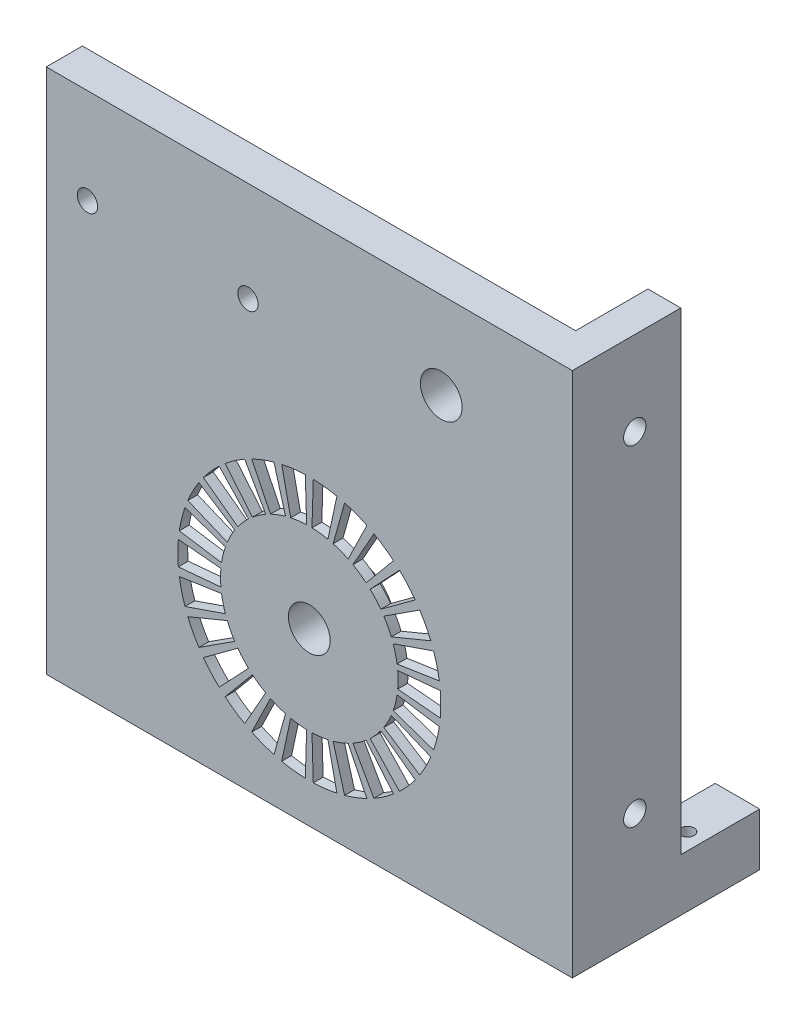
SolidWorks part; units mm, degrees
ref_plane "Front Plane" through (0, 0, 0) normal (0, 0, 1) x (1, 0, 0)
ref_plane "Top Plane" through (0, 0, 0) normal (0, 1, 0) x (1, 0, 0)
ref_plane "Right Plane" through (0, 0, 0) normal (1, 0, 0) x (0, 0, -1)
sketch "LED panel" plane through (0, 0, 0) normal (0, 0, 1) x (1, 0, 0)
  line L1 (-40, 40) -> (40, 40)
  line L2 (-40, 40) -> (-40, -40)
  line L3 (-40, -40) -> (40, -40)
  line L4 (40, 40) -> (40, -40)
  line L5 (-40, 40) -> (40, -40) construction
  line L6 (-40, -40) -> (40, 40) construction
  point P0 (0, 0)
  dimension "D1" = 80
  dimension "D2" = 80
extrude "Extrude LED panel" add sketch "LED panel" along normal blind 2.5
sketch "Sketch3" plane through (0, 0, 2.5) normal (0, 0, 1) x (1, 0, 0)
  circle A0 centre (0, -14) radius 5.9987
  circle A1 centre (20.0721, 26.7806) radius 6.0029
extrude "Boss-Extrude2" add sketch "Sketch3" against normal blind 7
sketch "Sketch1" plane through (0, 0, 2.5) normal (0, 0, 1) x (1, 0, 0)
  line L0 (-40, -14) -> (40, -14) construction
  line L3 (0, 40) -> (0, -40) construction
  line L4 (40, 40) -> (-40, 40) construction
  line L5 (-40, -40) -> (40, -40) construction
  line L6 (0, -14) -> (52.2337, -7.6577) construction
  line L7 (0, -14) -> (47.0949, -19.7184) construction
  line L8 (0, -14) -> (19.9179, -12.19) construction
  line L9 (0, -14) -> (41.9979, -17.8164) construction
  line L10 (13.4446, -12.7783) -> (19.9179, -12.19)
  line L11 (13.4446, -15.2217) -> (19.9179, -15.81)
  line L12 (13.3463, -16.0313) -> (19.7723, -17.0093)
  line L13 (12.7615, -18.4037) -> (18.906, -20.5241)
  line L14 (12.4724, -19.1662) -> (18.4776, -21.6537)
  line L15 (11.3368, -21.3298) -> (16.7953, -24.859)
  line L16 (10.8736, -22.0009) -> (16.109, -25.8532)
  line L17 (9.2533, -23.8299) -> (13.7085, -28.5628)
  line L18 (8.6429, -24.3707) -> (12.8043, -29.364)
  line L19 (6.6319, -25.7587) -> (9.8251, -31.4203)
  line L20 (5.9099, -26.1377) -> (8.7554, -31.9818)
  line L21 (3.6252, -27.0042) -> (5.3706, -33.2654)
  line L22 (2.8334, -27.1993) -> (4.1976, -33.5545)
  line L23 (0.4077, -27.4938) -> (0.6041, -33.9909)
  line L24 (-0.4077, -27.4938) -> (-0.6041, -33.9909)
  line L25 (-2.8334, -27.1993) -> (-4.1976, -33.5545)
  line L26 (-3.6252, -27.0042) -> (-5.3706, -33.2654)
  line L27 (-5.9099, -26.1377) -> (-8.7554, -31.9818)
  line L28 (-6.6319, -25.7587) -> (-9.8251, -31.4203)
  line L29 (-8.6429, -24.3707) -> (-12.8043, -29.364)
  line L30 (-9.2533, -23.8299) -> (-13.7085, -28.5628)
  line L31 (-10.8736, -22.0009) -> (-16.109, -25.8532)
  line L32 (-11.3368, -21.3298) -> (-16.7953, -24.859)
  line L33 (-12.4724, -19.1662) -> (-18.4776, -21.6537)
  line L34 (-12.7615, -18.4037) -> (-18.906, -20.5241)
  line L35 (-13.3463, -16.0313) -> (-19.7723, -17.0093)
  line L36 (-13.4446, -15.2217) -> (-19.9179, -15.81)
  line L37 (-13.4446, -12.7783) -> (-19.9179, -12.19)
  line L38 (-13.3463, -11.9687) -> (-19.7723, -10.9907)
  line L39 (-12.7615, -9.5963) -> (-18.906, -7.4759)
  line L40 (-12.4724, -8.8338) -> (-18.4776, -6.3463)
  line L41 (-11.3368, -6.6702) -> (-16.7953, -3.141)
  line L42 (-10.8736, -5.9991) -> (-16.109, -2.1468)
  line L43 (-9.2533, -4.1701) -> (-13.7085, 0.5628)
  line L44 (-8.6429, -3.6293) -> (-12.8043, 1.364)
  line L45 (-6.6319, -2.2413) -> (-9.8251, 3.4203)
  line L46 (-5.9099, -1.8623) -> (-8.7554, 3.9818)
  line L47 (-3.6252, -0.9958) -> (-5.3706, 5.2654)
  line L48 (-2.8334, -0.8007) -> (-4.1976, 5.5545)
  line L49 (-0.4077, -0.5062) -> (-0.6041, 5.9909)
  line L50 (0.4077, -0.5062) -> (0.6041, 5.9909)
  line L51 (2.8334, -0.8007) -> (4.1976, 5.5545)
  line L52 (3.6252, -0.9958) -> (5.3706, 5.2654)
  line L53 (5.9099, -1.8623) -> (8.7554, 3.9818)
  line L54 (6.6319, -2.2413) -> (9.8251, 3.4203)
  line L55 (8.6429, -3.6293) -> (12.8043, 1.364)
  line L56 (9.2533, -4.1701) -> (13.7085, 0.5628)
  line L57 (10.8736, -5.9991) -> (16.109, -2.1468)
  line L58 (11.3368, -6.6702) -> (16.7953, -3.141)
  line L59 (12.4724, -8.8338) -> (18.4776, -6.3463)
  line L60 (12.7615, -9.5963) -> (18.906, -7.4759)
  line L61 (13.3463, -11.9687) -> (19.7723, -10.9907)
  line L62 (-40, -40) -> (40, -40) construction
  line L63 (40, -40) -> (40, 40) construction
  line L64 (-40, 40) -> (-40, -40) construction
  arc A0 (19.9179, -15.81) -> (19.9179, -12.19) centre (0, -14) ccw
  arc A1 (13.4446, -15.2217) -> (13.4446, -12.7783) centre (0, -14) ccw
  arc A2 (18.906, -20.5241) -> (19.7723, -17.0093) centre (0, -14) ccw
  arc A3 (12.7615, -18.4037) -> (13.3463, -16.0313) centre (0, -14) ccw
  arc A4 (16.7953, -24.859) -> (18.4776, -21.6537) centre (0, -14) ccw
  arc A5 (11.3368, -21.3298) -> (12.4724, -19.1662) centre (0, -14) ccw
  arc A6 (13.7085, -28.5628) -> (16.109, -25.8532) centre (0, -14) ccw
  arc A7 (9.2533, -23.8299) -> (10.8736, -22.0009) centre (0, -14) ccw
  arc A8 (9.8251, -31.4203) -> (12.8043, -29.364) centre (0, -14) ccw
  arc A9 (6.6319, -25.7587) -> (8.6429, -24.3707) centre (0, -14) ccw
  arc A10 (5.3706, -33.2654) -> (8.7554, -31.9818) centre (0, -14) ccw
  arc A11 (3.6252, -27.0042) -> (5.9099, -26.1377) centre (0, -14) ccw
  arc A12 (0.6041, -33.9909) -> (4.1976, -33.5545) centre (0, -14) ccw
  arc A13 (0.4077, -27.4938) -> (2.8334, -27.1993) centre (0, -14) ccw
  arc A14 (-4.1976, -33.5545) -> (-0.6041, -33.9909) centre (0, -14) ccw
  arc A15 (-2.8334, -27.1993) -> (-0.4077, -27.4938) centre (0, -14) ccw
  arc A16 (-8.7554, -31.9818) -> (-5.3706, -33.2654) centre (0, -14) ccw
  arc A17 (-5.9099, -26.1377) -> (-3.6252, -27.0042) centre (0, -14) ccw
  arc A18 (-12.8043, -29.364) -> (-9.8251, -31.4203) centre (0, -14) ccw
  arc A19 (-8.6429, -24.3707) -> (-6.6319, -25.7587) centre (0, -14) ccw
  arc A20 (-16.109, -25.8532) -> (-13.7085, -28.5628) centre (0, -14) ccw
  arc A21 (-10.8736, -22.0009) -> (-9.2533, -23.8299) centre (0, -14) ccw
  arc A22 (-18.4776, -21.6537) -> (-16.7953, -24.859) centre (0, -14) ccw
  arc A23 (-12.4724, -19.1662) -> (-11.3368, -21.3298) centre (0, -14) ccw
  arc A24 (-19.7723, -17.0093) -> (-18.906, -20.5241) centre (0, -14) ccw
  arc A25 (-13.3463, -16.0313) -> (-12.7615, -18.4037) centre (0, -14) ccw
  arc A26 (-19.9179, -12.19) -> (-19.9179, -15.81) centre (0, -14) ccw
  arc A27 (-13.4446, -12.7783) -> (-13.4446, -15.2217) centre (0, -14) ccw
  arc A28 (-18.906, -7.4759) -> (-19.7723, -10.9907) centre (0, -14) ccw
  arc A29 (-12.7615, -9.5963) -> (-13.3463, -11.9687) centre (0, -14) ccw
  arc A30 (-16.7953, -3.141) -> (-18.4776, -6.3463) centre (0, -14) ccw
  arc A31 (-11.3368, -6.6702) -> (-12.4724, -8.8338) centre (0, -14) ccw
  arc A32 (-13.7085, 0.5628) -> (-16.109, -2.1468) centre (0, -14) ccw
  arc A33 (-9.2533, -4.1701) -> (-10.8736, -5.9991) centre (0, -14) ccw
  arc A34 (-9.8251, 3.4203) -> (-12.8043, 1.364) centre (0, -14) ccw
  arc A35 (-6.6319, -2.2413) -> (-8.6429, -3.6293) centre (0, -14) ccw
  arc A36 (-5.3706, 5.2654) -> (-8.7554, 3.9818) centre (0, -14) ccw
  arc A37 (-3.6252, -0.9958) -> (-5.9099, -1.8623) centre (0, -14) ccw
  arc A38 (-0.6041, 5.9909) -> (-4.1976, 5.5545) centre (0, -14) ccw
  arc A39 (-0.4077, -0.5062) -> (-2.8334, -0.8007) centre (0, -14) ccw
  arc A40 (4.1976, 5.5545) -> (0.6041, 5.9909) centre (0, -14) ccw
  arc A41 (2.8334, -0.8007) -> (0.4077, -0.5062) centre (0, -14) ccw
  arc A42 (8.7554, 3.9818) -> (5.3706, 5.2654) centre (0, -14) ccw
  arc A43 (5.9099, -1.8623) -> (3.6252, -0.9958) centre (0, -14) ccw
  arc A44 (12.8043, 1.364) -> (9.8251, 3.4203) centre (0, -14) ccw
  arc A45 (8.6429, -3.6293) -> (6.6319, -2.2413) centre (0, -14) ccw
  arc A46 (16.109, -2.1468) -> (13.7085, 0.5628) centre (0, -14) ccw
  arc A47 (10.8736, -5.9991) -> (9.2533, -4.1701) centre (0, -14) ccw
  arc A48 (18.4776, -6.3463) -> (16.7953, -3.141) centre (0, -14) ccw
  arc A49 (12.4724, -8.8338) -> (11.3368, -6.6702) centre (0, -14) ccw
  arc A50 (19.7723, -10.9907) -> (18.906, -7.4759) centre (0, -14) ccw
  arc A51 (13.3463, -11.9687) -> (12.7615, -9.5963) centre (0, -14) ccw
  circle A52 centre (0, -14) radius 3.175
  point P124 (0, -14)
  dimension "D2" = 40
  dimension "D9" = 6.35
  dimension "D1" = 6.923
  dimension "D3" = 6.923
  dimension "D4" = 6.5
  dimension "D5" = 5.192
  dimension "D6" = 5.192
  dimension "D8" = 26
  dimension "D7" = 26
extrude "Cut arrow indication holes" cut sketch "Sketch1" against normal through all
sketch "Sketch4" plane through (0, 0, 0) normal (0, 0, 1) x (1, 0, 0)
  circle A0 centre (20.0721, 26.7806) radius 3.175
  dimension "D1" = 6.35
  dimension "D2" = 20.0721
  dimension "D3" = 26.7806
extrude "Cut hole for secondary rod" cut sketch "Sketch4" along normal through all and the other way blind 7
sketch "Sketch2" plane through (0, 0, 0) normal (0, 0, -1) x (-1, 0, 0)
  line L0 (-1, 13.4818) -> (-1, 14.9818)
  line L1 (-1, 14.9818) -> (1, 14.9818)
  line L2 (1, 14.9818) -> (1, 13.4818)
  line L3 (0, -14) -> (0, 30.4199) construction
  line L4 (-8.9582, -40) -> (8.9582, -40)
  line L5 (40, -40) -> (-40, -40) construction
  arc A0 (-1, 13.4818) -> (-8.9582, -40) centre (0, -14) ccw
  arc A1 (8.9582, -40) -> (1, 13.4818) centre (0, -14) ccw
  circle A2 centre (0, -14) radius 5.9987
  point P5 (0, 14.9818)
  dimension "D1" = 55
  dimension "D2" = 2
  dimension "D3" = 1.5
extrude "Cut slot for PCB" cut sketch "Sketch2" against normal blind 1
sketch "Sketch6" plane through (0, 0, 0) normal (0, 0, -1) x (-1, 0, 0)
  line L0 (40, 40) -> (40, -40) construction
  line L1 (-40, 40) -> (40, 40)
  line L2 (-40, 40) -> (-40, 37)
  line L3 (-40, 37) -> (8.9219, 37)
  line L4 (40, 40) -> (40, -40)
  line L5 (37, 37) -> (37, -40)
  line L6 (8.9219, 37) -> (-40, 5.5647)
  line L7 (-40, -40) -> (-40, 40) construction
  line L8 (14.4714, 37) -> (-40, 1.9987)
  line L9 (40, -40) -> (8.9582, -40) construction
  line L10 (14.4714, 37) -> (37, 37)
  line L11 (-40, 5.5647) -> (-40, 1.9987)
  line L12 (40, -40) -> (37, -40)
  dimension "D1" = 3
  dimension "D2" = 3
  dimension "D3" = 3
extrude "Boss-Extrude3" add sketch "Sketch6" along normal blind 3
sketch "Sketch9" plane through (40, 0, 0) normal (1, 0, 0) x (0, 0, -1)
  line L0 (3, 40) -> (3, 37) construction
  line L1 (-2.5, 40) -> (14, 40)
  line L2 (-2.5, 40) -> (-2.5, -40)
  line L3 (-2.5, -40) -> (14, -40)
  line L4 (14, 40) -> (14, -40)
  dimension "D1" = 11
extrude "Boss-Extrude4" add sketch "Sketch9" against normal blind 5
sketch "Sketch11" plane through (0, 0, -14) normal (0, 0, -1) x (-1, 0, 0)
  line L0 (-35, -40) -> (-35, 40) construction
  line L1 (-40, -40) -> (-35, -40)
  line L2 (-40, -40) -> (-40, -32)
  line L3 (-40, -32) -> (-33.2309, -32)
  line L4 (-35, -40) -> (-33.2309, -32)
  dimension "D1" = 8
extrude "Boss-Extrude5" add sketch "Sketch11" along normal blind 12 and the other way up to surface (16.5 mm away)
sketch "Sketch12" plane through (0, -32, 0) normal (0, 1, 0) x (1, 0, 0)
  line L0 (33.2309, 0) -> (35, 0) construction
  line L1 (40, 14) -> (40, 26) construction
  circle A0 centre (37.5, 17.53) radius 1
  dimension "D2" = 2.5
  dimension "D3" = 2
  dimension "D1" = 17.53
extrude "Cut-Extrude1" cut sketch "Sketch12" against normal through all
sketch "Sketch13" plane through (0, 0, 0) normal (0, 0, -1) x (-1, 0, 0)
  line L0 (40, 40) -> (-35, 40) construction
  line L1 (40, -40) -> (40, 40) construction
  circle A0 centre (33.74, 25.5) radius 3
  circle A1 centre (9.33, 24.81) radius 3
  dimension "D3" = 6
  dimension "D4" = 6
  dimension "D5" = 30.67
  dimension "D6" = 6.26
  dimension "D1" = 14.5
  dimension "D2" = 15.19
extrude "Boss-Extrude6" add sketch "Sketch13" along normal blind 3
sketch "Sketch14" plane through (0, 0, -3) normal (0, 0, -1) x (-1, 0, 0)
  circle A0 centre (33.74, 25.5) radius 1.55
  circle A1 centre (9.33, 24.81) radius 1.55
  dimension "D1" = 3.1
  dimension "D2" = 3.1
extrude "Cut-Extrude2" cut sketch "Sketch14" against normal through all
hole_wizard "CSK for M3 Flat Head Machine Screw1" positions "Sketch16" profile "Sketch15" countersink size "M3" standard "ANSI Metric"
sketch "Sketch16" plane through (35, 0, 0) normal (-1, 0, 0) x (0, 0, 1)
  line L0 (-14, -32) -> (-14, 40) construction
  line L3 (0, 30.1119) -> (-14, 30.1119) construction
  line L4 (0, 8.7775) -> (0, 37) construction
  line L6 (-7, 30.1119) -> (-7, -44.9803) construction
  point P0 (-7, 27.1971)
  point P2 (-7, -23.0779)
sketch "Sketch15" plane through (35, 27.1971, -7) normal (0, 1, 0) x (0, 0, 1)
  line L0 (0, 0) -> (0, 5)
  line L1 (0, 5) -> (1.7, 5)
  line L2 (1.7, 5) -> (1.7, 1.45)
  line L3 (1.7, 1.45) -> (3.15, 0)
  line L5 (3.15, 0) -> (0, 0)
  line L6 (-1.7, 1.45) -> (-3.15, 0) construction
  line L11 (0, -6.35) -> (0, 107.95) construction
  dimension "Thru Hole Dia." = 3.4
  dimension "Thru Hole Depth" = 5
  dimension "Near C'Sink Dia." = 6.3
  dimension "Near C'Sink Angle" = 90
equation "\"D6@Sketch1\"=3/4*360/2/26"
